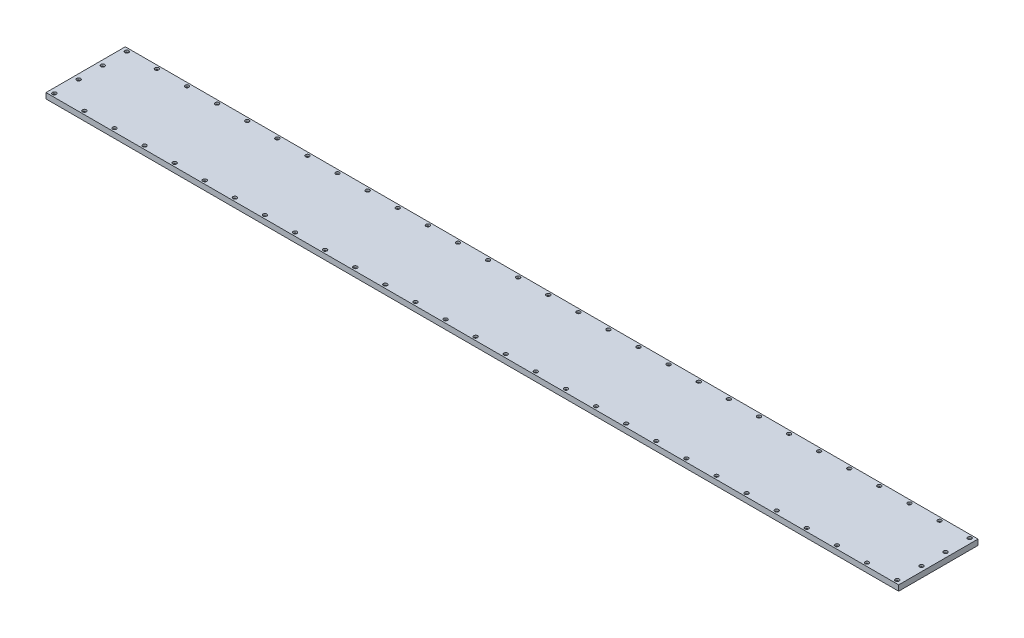
SolidWorks part; units mm, degrees
ref_plane "Front Plane" through (0, 0, 0) normal (0, 0, 1) x (1, 0, 0)
ref_plane "Top Plane" through (0, 0, 0) normal (0, 1, 0) x (1, 0, 0)
ref_plane "Right Plane" through (0, 0, 0) normal (1, 0, 0) x (0, 0, -1)
sketch "Sketch2" plane through (0, 0, 0) normal (0, 1, 0) x (1, 0, 0)
  line L1 (-537.5, -50) -> (537.5, -50)
  line L2 (-537.5, -50) -> (-537.5, 50)
  line L3 (-537.5, 50) -> (537.5, 50)
  line L4 (537.5, -50) -> (537.5, 50)
  line L5 (-537.5, -50) -> (537.5, 50) construction
  line L6 (-537.5, 50) -> (537.5, -50) construction
  point P0 (0, 0)
  dimension "D1" = 1075
  dimension "D2" = 100
extrude "Boss-Extrude1" add sketch "Sketch2" along normal blind 7
sketch "Sketch3" plane through (0, 7, 0) normal (0, 1, 0) x (1, 0, 0)
  line L0 (531.25, 45.75) -> (531.25, 50) construction
  line L1 (537.5, 50) -> (-537.5, 50) construction
  line L2 (531.25, 45.75) -> (537.5, 45.75) construction
  line L3 (537.5, -50) -> (537.5, 50) construction
  circle A0 centre (531.25, 45.75) radius 1.7
  dimension "D1" = 4.25
  dimension "D2" = 6.25
extrude "Cut-Extrude1" cut sketch "Sketch3" against normal through all
sketch "Sketch4" plane through (0, 7, 0) normal (0, 1, 0) x (1, 0, 0)
  circle A0 centre (531.25, 45.75) radius 2.4
extrude "Cut-Extrude2" cut sketch "Sketch4" against normal blind 2.5
pattern_linear "LPattern1" count 4 spacing 30.425 along (0, 0, 1) of "Cut-Extrude2", "Cut-Extrude1"
ref_plane "Plane1" through (0, 0, 0) normal (1, 0, 0) x (0, 0, -1)
mirror "Mirror1" about plane through (0, 0, 0) normal (1, 0, 0) of "Cut-Extrude1", "Cut-Extrude2", "LPattern1"
pattern_linear "LPattern2" count 29 spacing 37.95 along (-1, 0, 0) of "Cut-Extrude1", "Cut-Extrude2"
ref_plane "Plane2" through (0, 0, 0) normal (0, 0, -1) x (-1, 0, 0)
mirror "Mirror2" about plane through (0, 0, 0) normal (0, 0, -1) of "LPattern2", "Cut-Extrude1", "Cut-Extrude2"
